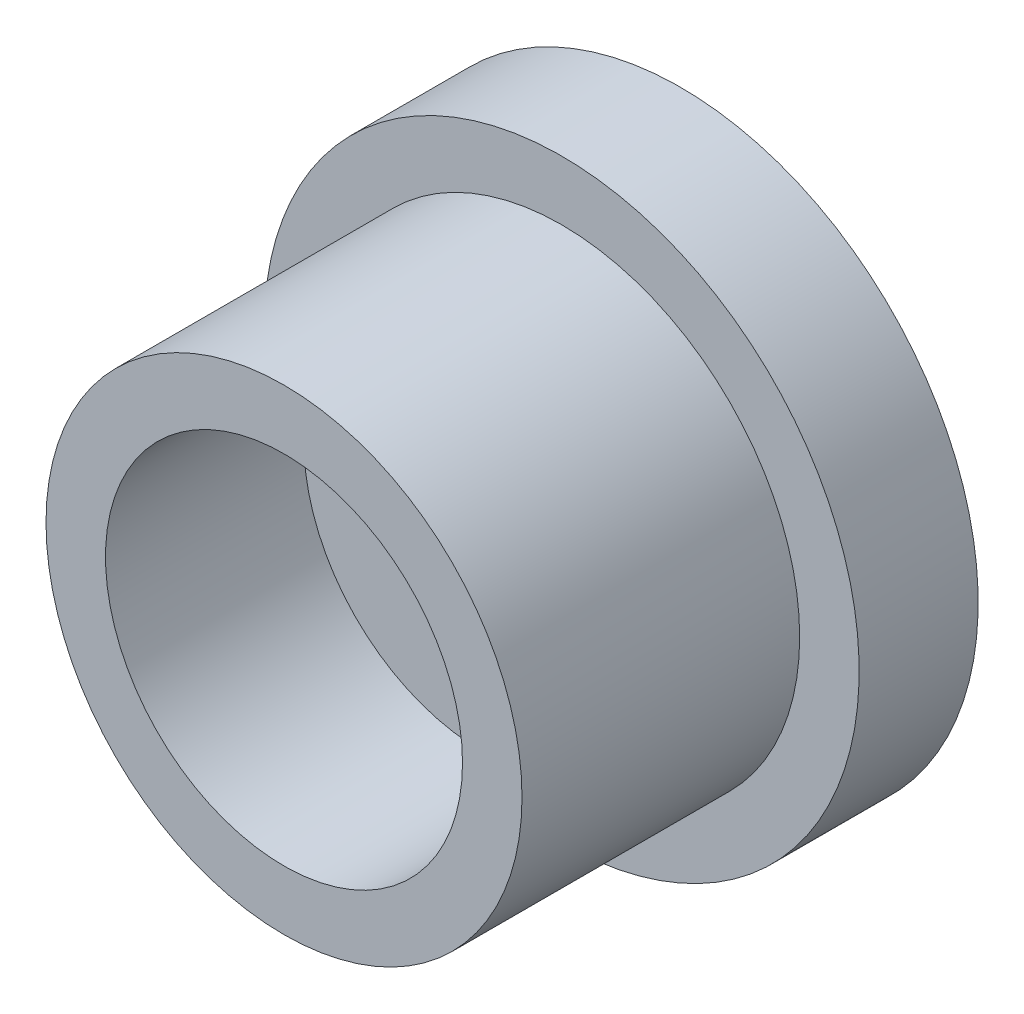
SolidWorks part; units mm, degrees
ref_plane "Piano frontale" through (0, 0, 0) normal (0, 0, 1) x (1, 0, 0)
ref_plane "Piano superiore" through (0, 0, 0) normal (0, 1, 0) x (1, 0, 0)
ref_plane "Piano destro" through (0, 0, 0) normal (1, 0, 0) x (0, 0, -1)
sketch "Schizzo1" plane through (0, 0, 0) normal (0, 0, 1) x (1, 0, 0)
  circle A0 centre (0, 0) radius 6
  dimension "D1" = 12
extrude "Estrusione-Estrusione1" add sketch "Schizzo1" along normal blind 7
sketch "Schizzo2" plane through (0, 0, 7) normal (0, 0, 1) x (1, 0, 0)
  circle A0 centre (0, 0) radius 4.5
  dimension "D1" = 9
extrude "Taglio-Estrusione1" cut sketch "Schizzo2" against normal blind 5
sketch "Schizzo3" plane through (0, 0, 0) normal (0, 0, -1) x (-1, 0, 0)
  circle A0 centre (0, 0) radius 7.5
  dimension "D1" = 15
extrude "Estrusione-Estrusione2" add sketch "Schizzo3" along normal blind 3
